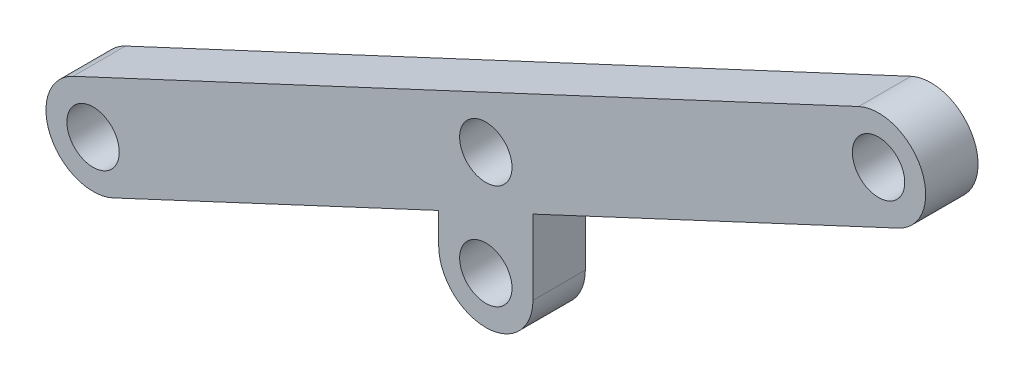
SolidWorks part; units mm, degrees
material "6061 合金"
ref_plane "前视基准面" through (0, 0, 0) normal (0, 0, 1) x (1, 0, 0)
ref_plane "上视基准面" through (0, 0, 0) normal (0, 1, 0) x (1, 0, 0)
ref_plane "右视基准面" through (0, 0, 0) normal (1, 0, 0) x (0, 0, -1)
sketch "草图1" plane through (0, 0, 0) normal (0, 0, 1) x (1, 0, 0)
  line L0 (0, -5) -> (0, 5) construction
  line L1 (-4.5, -5) -> (-4.5, 5)
  line L2 (4.5, -5) -> (4.5, 5)
  arc A0 (-4.5, -5) -> (4.5, -5) centre (0, -5) ccw
  arc A1 (4.5, 5) -> (-4.5, 5) centre (0, 5) ccw
  circle A2 centre (0, 5) radius 2.5
  circle A3 centre (0, -5) radius 2.5
  point P2 (0, 0)
  dimension "D1" = 10
  dimension "D2" = 2
  dimension "D3" = 5
extrude "凸台-拉伸1" add sketch "草图1" along normal mid plane 5
sketch "草图2" plane through (0, 0, 2.5) normal (0, 0, 1) x (1, 0, 0)
  line L0 (-37.5, -12.5) -> (37.5, 22.5) construction
  line L1 (-39.403, -8.4222) -> (35.597, 26.5778)
  line L2 (-35.597, -16.5778) -> (39.403, 18.4222)
  arc A0 (-39.403, -8.4222) -> (-35.597, -16.5778) centre (-37.5, -12.5) ccw
  arc A1 (39.403, 18.4222) -> (35.597, 26.5778) centre (37.5, 22.5) ccw
  arc A2 (4.5, 5) -> (-4.5, 5) centre (0, 5) ccw construction
  circle A3 centre (-37.5, -12.5) radius 2.5
  circle A4 centre (37.5, 22.5) radius 2.5
  circle A5 centre (0, 5) radius 2.5 construction
  circle A6 centre (0, 5) radius 2.5
  point P2 (0, 5)
  dimension "D1" = 75
  dimension "D2" = 35
extrude "凸台-拉伸2" add sketch "草图2" against normal up to surface (5 mm away) up to face at (2.5, 5, -2.5)
